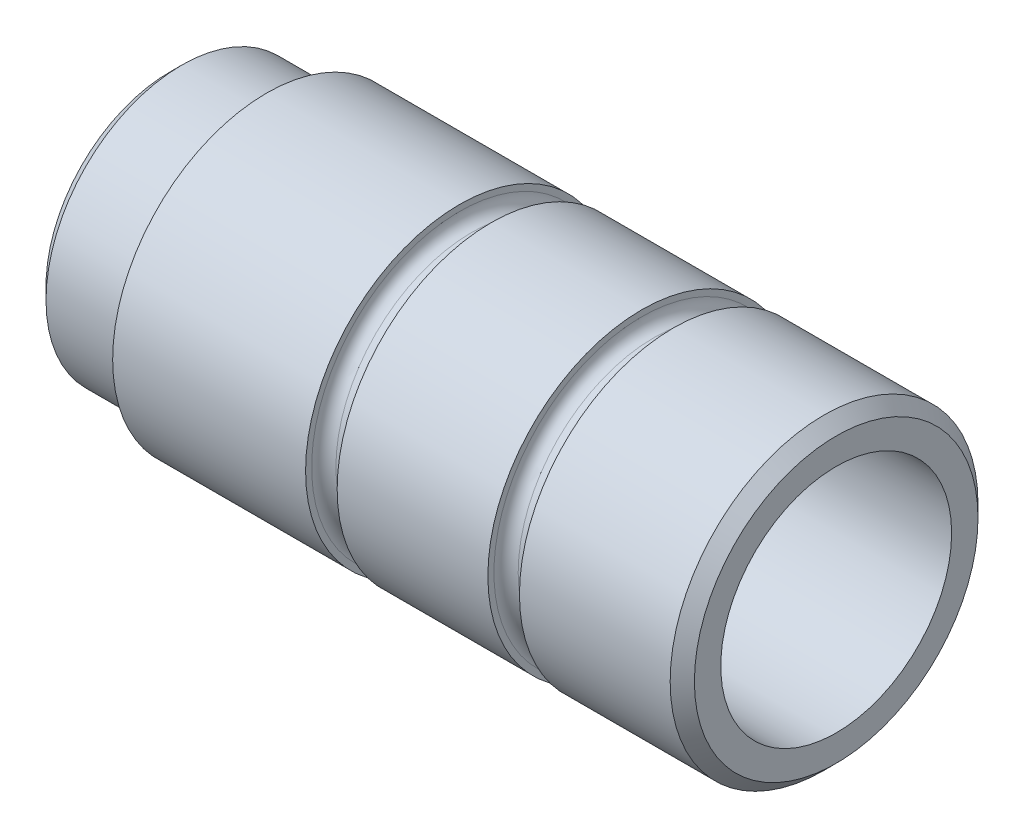
SolidWorks part; units mm, degrees
material "Plain Carbon Steel"
ref_plane "Front Plane" through (0, 0, 0) normal (0, 0, 1) x (1, 0, 0)
ref_plane "Top Plane" through (0, 0, 0) normal (0, 1, 0) x (1, 0, 0)
ref_plane "Right Plane" through (0, 0, 0) normal (1, 0, 0) x (0, 0, -1)
sketch "Sketch1" plane through (0, 0, 0) normal (0, 0, 1) x (1, 0, 0)
  line L0 (19.1683, 0) -> (-88.2055, 0) construction
  line L1 (0, 9.525) -> (-55, 9.525)
  line L2 (0, 9.525) -> (0, 11.7)
  line L3 (-1, 12.7) -> (-13.4361, 12.7)
  line L4 (-13.4361, 12.7) -> (-13.4361, 12.2)
  line L5 (-14.4361, 11.2) -> (-15.041, 11.2)
  line L6 (-16.041, 12.2) -> (-16.041, 12.7)
  line L7 (-16.041, 12.7) -> (-28.4771, 12.7)
  line L8 (-28.4771, 12.7) -> (-28.4771, 12.2)
  line L9 (-29.4771, 11.2) -> (-30.0821, 11.2)
  line L10 (-31.0821, 12.2) -> (-31.0821, 12.7)
  line L11 (-31.0821, 12.7) -> (-47, 12.7)
  line L12 (-47, 12.7) -> (-47, 12.2)
  line L13 (-48, 11.2) -> (-54, 11.2)
  line L14 (-55, 10.2) -> (-55, 9.525)
  line L15 (-54, 11.2) -> (-55, 10.2)
  line L16 (0, 11.7) -> (-1, 12.7)
  arc A0 (-13.4361, 12.2) -> (-14.4361, 11.2) centre (-14.4361, 12.2) cw
  arc A1 (-16.041, 12.2) -> (-15.041, 11.2) centre (-15.041, 12.2) ccw
  arc A2 (-29.4771, 11.2) -> (-28.4771, 12.2) centre (-29.4771, 12.2) ccw
  arc A3 (-31.0821, 12.2) -> (-30.0821, 11.2) centre (-30.0821, 12.2) ccw
  arc A4 (-47, 12.2) -> (-48, 11.2) centre (-48, 12.2) cw
  point P6 (0, 12.7)
  point P15 (-55, 11.2)
  dimension "D4" = 1
  dimension "D5" = 1
  dimension "D1" = 19.05
  dimension "D2" = 25.4
  dimension "D3" = 1.5
  dimension "D6" = 8
  dimension "D7" = 55
revolve "Revolve1" add sketch "Sketch1"
